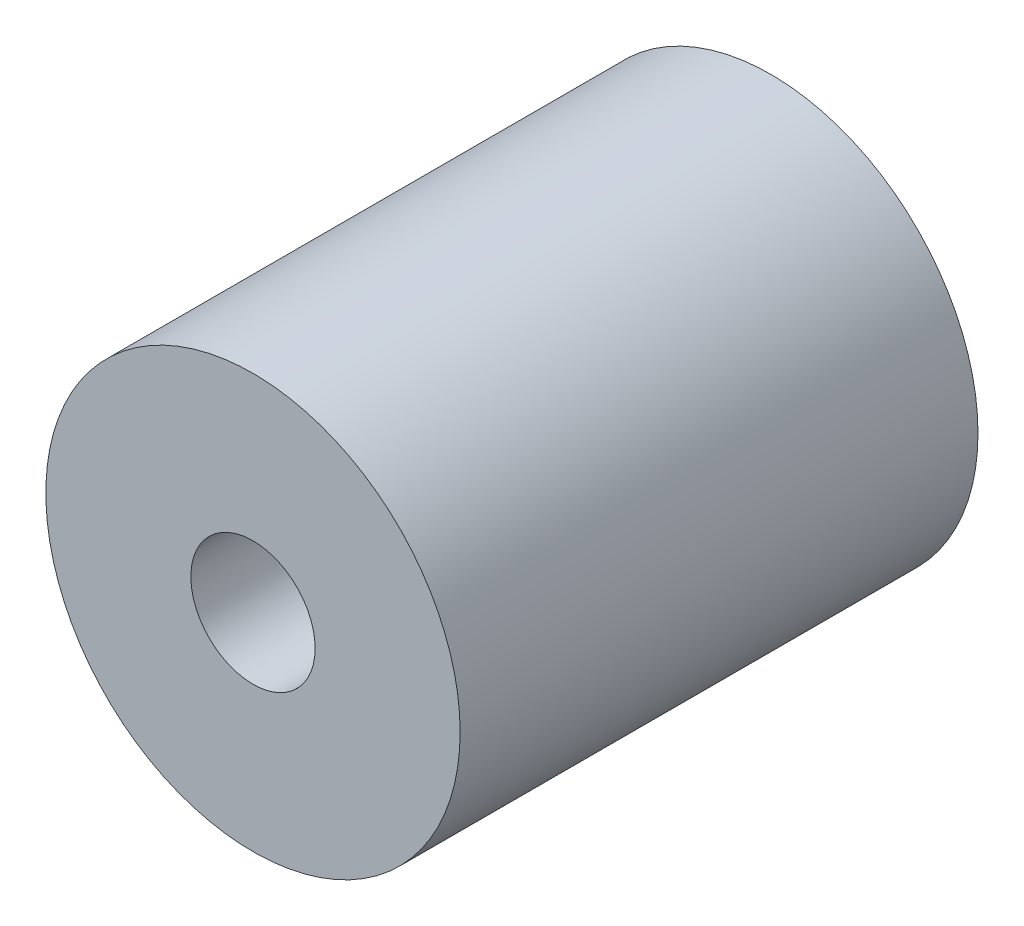
SolidWorks part; units mm, degrees
ref_plane "Plan de face" through (0, 0, 0) normal (0, 0, 1) x (1, 0, 0)
ref_plane "Plan de dessus" through (0, 0, 0) normal (0, 1, 0) x (1, 0, 0)
ref_plane "Plan de droite" through (0, 0, 0) normal (1, 0, 0) x (0, 0, -1)
sketch "Esquisse1" plane through (0, 0, 0) normal (0, 0, 1) x (1, 0, 0)
  circle A0 centre (0, 0) radius 10
  circle A1 centre (0, 0) radius 3
  dimension "D1" = 6
  dimension "D2" = 20
extrude "Boss.-Extru.1" add sketch "Esquisse1" along normal blind 25
